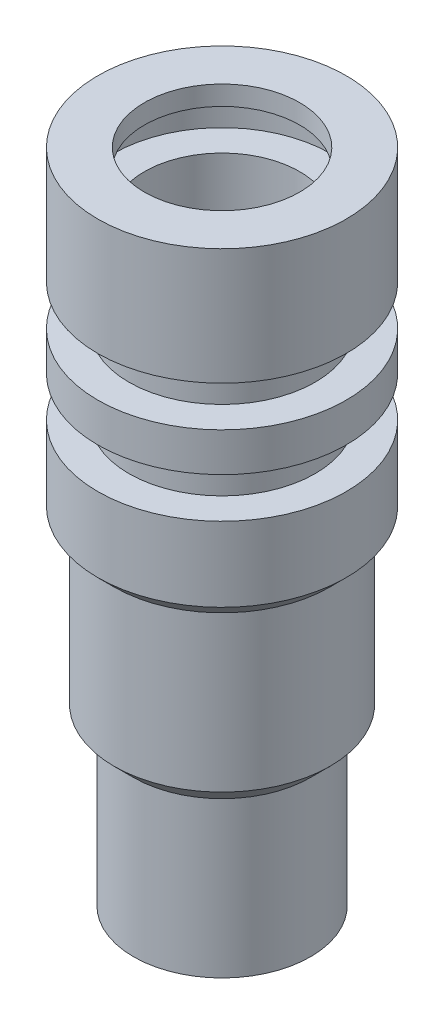
SolidWorks part; units mm, degrees
ref_plane "Front Plane" through (0, 0, 0) normal (0, 0, 1) x (1, 0, 0)
ref_plane "Top Plane" through (0, 0, 0) normal (0, 1, 0) x (1, 0, 0)
ref_plane "Right Plane" through (0, 0, 0) normal (1, 0, 0) x (0, 0, -1)
sketch "Sketch1" plane through (0, 0, 0) normal (0, 0, 1) x (1, 0, 0)
  line L0 (0, 0) -> (0, -47.1867) construction
  line L1 (-6.35, 0) -> (-10.16, 0)
  line L2 (-10.16, -19.304) -> (-10.16, -25.4)
  line L3 (-10.16, -25.4) -> (-8.8265, -26.7335)
  line L4 (-8.8265, -26.7335) -> (-8.8265, -39.4335)
  line L5 (-8.8265, -39.4335) -> (-7.239, -41.021)
  line L6 (-7.239, -41.021) -> (-7.239, -53.721)
  line L7 (-7.239, -53.721) -> (-6.35, -53.721)
  line L8 (-6.35, -53.721) -> (-6.35, -4.8895)
  line L9 (-10.16, 0) -> (-10.16, -9.525)
  line L10 (-10.16, -9.525) -> (-7.62, -9.525)
  line L11 (-7.62, -9.525) -> (-7.62, -12.827)
  line L12 (-7.62, -12.827) -> (-10.16, -12.827)
  line L13 (-10.16, -12.827) -> (-10.16, -16.002)
  line L14 (-10.16, -16.002) -> (-7.62, -16.002)
  line L15 (-7.62, -16.002) -> (-7.62, -19.304)
  line L16 (-7.62, -19.304) -> (-10.16, -19.304)
  line L17 (-6.35, 0) -> (-6.35, -1.5875)
  line L18 (-6.35, -1.5875) -> (-8.89, -1.5875)
  line L19 (-8.89, -1.5875) -> (-8.89, -4.8895)
  line L20 (-8.89, -4.8895) -> (-6.35, -4.8895)
  point P16 (-6.35, -5.0503)
  point P20 (-6.35, -9.6223)
  dimension "D1" = 135
  dimension "D2" = 6.35
  dimension "D3" = 0.889
  dimension "D4" = 1.5875
  dimension "D5" = 10.16
  dimension "D6" = 25.4
  dimension "D7" = 12.7
  dimension "D8" = 12.7
  dimension "D9" = 2.54
  dimension "D10" = 3.175
  dimension "D11" = 3.302
  dimension "D12" = 3.302
  dimension "D13" = 2.54
  dimension "D14" = 3.302
  dimension "D15" = 9.525
  dimension "D17" = 1.5875
revolve "Revolve1" add sketch "Sketch1" angle 360 about L0
